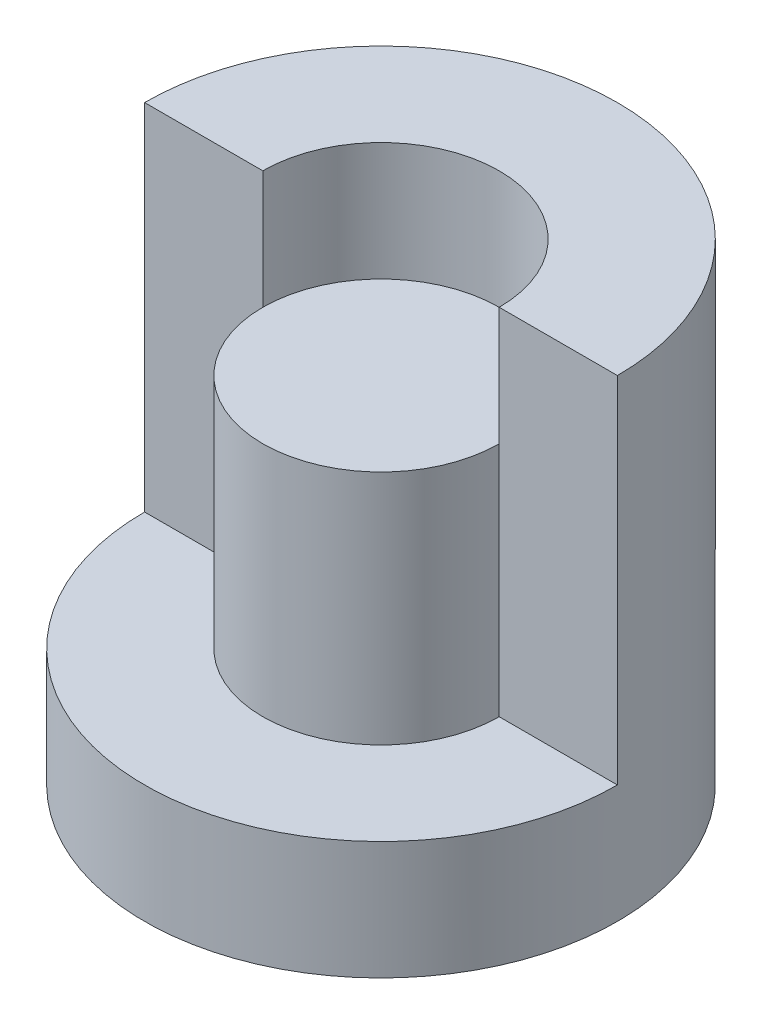
SolidWorks part; units mm, degrees
ref_plane "Front Plane" through (0, 0, 0) normal (0, 0, 1) x (1, 0, 0)
ref_plane "Top Plane" through (0, 0, 0) normal (0, 1, 0) x (1, 0, 0)
ref_plane "Right Plane" through (0, 0, 0) normal (1, 0, 0) x (0, 0, -1)
sketch "Sketch1" plane through (0, 0, 0) normal (0, 0, 1) x (1, 0, 0)
  line L1 (0, 0) -> (10, 0)
  line L2 (0, 0) -> (0, 20)
  line L3 (0, 20) -> (10, 20)
  line L4 (10, 0) -> (10, 20)
  dimension "D1" = 20
  dimension "D2" = 10
revolve "Revolve1" add sketch "Sketch1" angle 360 about L2
sketch "Sketch2" plane through (0, 20, 0) normal (0, 1, 0) x (1, 0, 0)
  circle A0 centre (0, 0) radius 5
  dimension "D1" = 10
extrude "Cut-Extrude5" cut sketch "Sketch2" against normal blind 5
sketch "Sketch5" plane through (0, 20, 0) normal (0, 1, 0) x (1, 0, 0)
  line L0 (-10, 0) -> (-5, 0)
  line L1 (5, 0) -> (10, 0)
  arc A0 (-10, 0) -> (10, 0) centre (0, 0) ccw
  circle A1 centre (0, 0) radius 10 construction
  arc A2 (-5, 0) -> (5, 0) centre (0, 0) ccw
  circle A3 centre (0, 0) radius 5 construction
  circle A4 centre (0, 0) radius 5 construction
  dimension "D3" = 5
  dimension "D4" = 10
  dimension "D1" = 5
  dimension "D2" = 5
extrude "Cut-Extrude6" cut sketch "Sketch5" against normal blind 15
